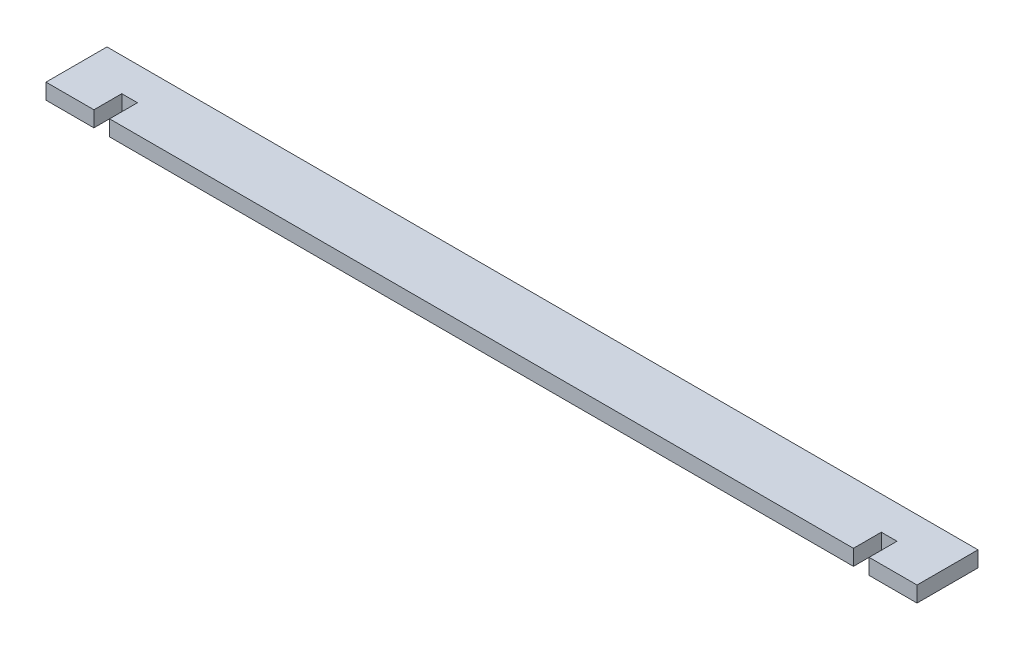
SolidWorks part; units mm, degrees
ref_plane "Front Plane" through (0, 0, 0) normal (0, 0, 1) x (1, 0, 0)
ref_plane "Top Plane" through (0, 0, 0) normal (0, 1, 0) x (1, 0, 0)
ref_plane "Right Plane" through (0, 0, 0) normal (1, 0, 0) x (0, 0, -1)
sketch "Sketch1" plane through (0, 0, 0) normal (0, 1, 0) x (1, 0, 0)
  line L0 (-500, 0) -> (-500, 70) construction
  line L1 (0, 0) -> (-55, 0)
  line L2 (0, 0) -> (0, 70)
  line L3 (0, 70) -> (-1000, 70)
  line L4 (-1000, 0) -> (-1000, 70)
  line L5 (-73, 0) -> (-927, 0)
  line L6 (-945, 0) -> (-945, 32)
  line L7 (-945, 32) -> (-927, 32)
  line L8 (-927, 0) -> (-927, 32)
  line L9 (-73, 0) -> (-73, 32)
  line L10 (-55, 0) -> (-55, 32)
  line L11 (-55, 32) -> (-73, 32)
  line L12 (-945, 0) -> (-1000, 0)
  point P5 (-500, 0)
  point P6 (-55, 0)
  point P7 (-945, 0)
  dimension "D1" = 1000
  dimension "D2" = 70
  dimension "D3" = 445
  dimension "D4" = 445
  dimension "D5" = 18
  dimension "D6" = 32
  dimension "D7" = 55
extrude "Boss-Extrude1" add sketch "Sketch1" along normal blind 18
